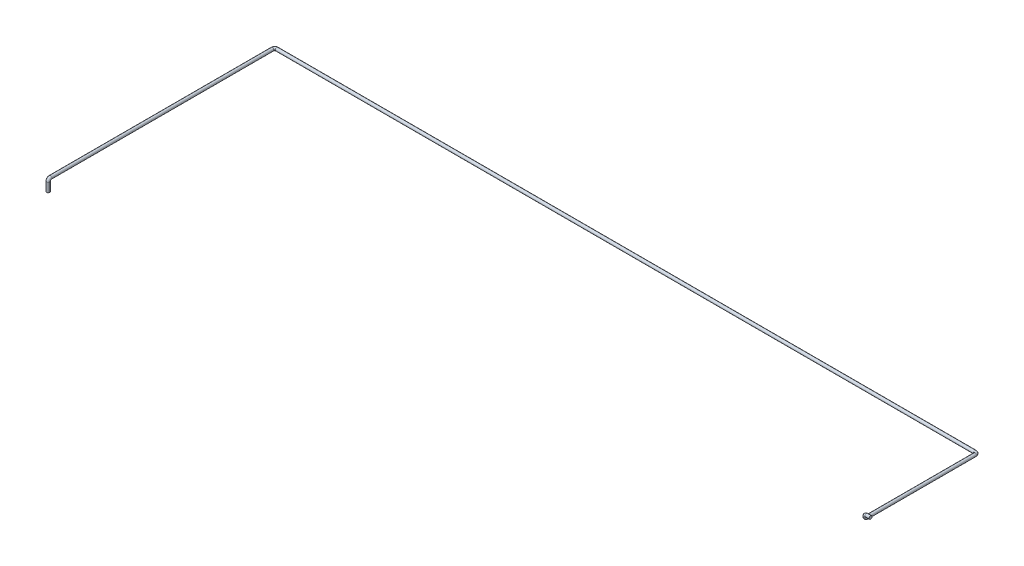
SolidWorks part; units mm, degrees
ref_plane "Alzado" through (0, 0, 0) normal (0, 0, 1) x (1, 0, 0)
ref_plane "Planta" through (0, 0, 0) normal (0, 1, 0) x (1, 0, 0)
ref_plane "Vista lateral" through (0, 0, 0) normal (1, 0, 0) x (0, 0, -1)
sketch3d "Croquis3D1"
  line L0 (0, 0, 0) -> (-36, 0, 0)
  line L1 (-50, -14, 0) -> (-50, -16, 0)
  line L2 (-50, -30, -14) -> (-50, -30, -980)
  line L3 (-70, -30, -1000) -> (-6295, -30, -1000)
  line L4 (-6315, -30, -980) -> (-6315, -30, 1000)
  line L5 (-6315, -50, 1020) -> (-6315, -130, 1020)
  arc A0 (-50, -16, 0) -> (-50, -30, -14) centre (-50, -16, -14) ccw
  arc A1 (-36, 0, 0) -> (-50, -14, 0) centre (-36, -14, 0) ccw
  arc A2 (-6315, -30, 1000) -> (-6315, -50, 1020) centre (-6315, -50, 1000) ccw
  arc A3 (-6295, -30, -1000) -> (-6315, -30, -980) centre (-6295, -30, -980) ccw
  arc A4 (-50, -30, -980) -> (-70, -30, -1000) centre (-70, -30, -980) ccw
  point P10 (-50, -30, 0)
  point P11 (-36, -16, -14)
  point P14 (-50, 0, 0)
  point P15 (-36, -14, 14)
  point P18 (-6315, -30, 1020)
  point P19 (-6295, -50, 1000)
  point P22 (-6315, -30, -1000)
  point P23 (-6295, -10, -980)
  point P26 (-50, -30, -1000)
  point P27 (-70, -10, -980)
  dimension "D7" = 14
  dimension "D8" = 20
  dimension "D1" = 50
  dimension "D2" = 30
  dimension "D3" = 1000
  dimension "D4" = 6265
  dimension "D5" = 2020
  dimension "D6" = 100
sketch "Croquis1" plane through (0, 0, 0) normal (1, 0, 0) x (0, 0, -1)
  circle A0 centre (0, 0) radius 13.7
  dimension "D1" = 27.4
sweep "Barrer1" add profiles "Croquis1" path "Croquis3D1"
